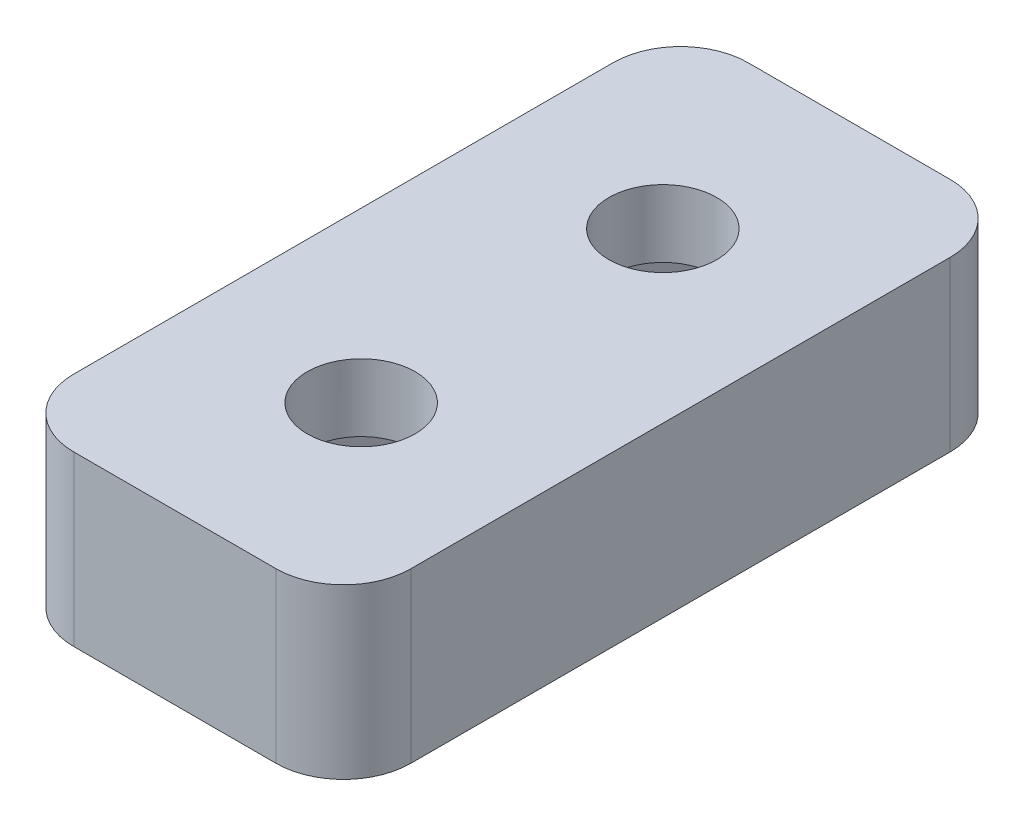
SolidWorks part; units mm, degrees
ref_plane "Alzado" through (0, 0, 0) normal (0, 0, 1) x (1, 0, 0)
ref_plane "Planta" through (0, 0, 0) normal (0, 1, 0) x (1, 0, 0)
ref_plane "Vista lateral" through (0, 0, 0) normal (1, 0, 0) x (0, 0, -1)
sketch "Croquis1" plane through (0, 0, 0) normal (0, 1, 0) x (1, 0, 0)
  line L0 (-5, 0) -> (5, 0) construction
  line L1 (-5, -10) -> (5, -10)
  line L2 (-5, -10) -> (-5, 10)
  line L3 (-5, 10) -> (5, 10)
  line L4 (5, -10) -> (5, 10)
  line L5 (-5, -10) -> (5, 10) construction
  line L6 (-5, 10) -> (5, -10) construction
  line L7 (0, 10) -> (0, -10) construction
  circle A0 centre (0, 4.4745) radius 1.6
  circle A1 centre (0, -4.4745) radius 1.6
  point P0 (0, 0)
  dimension "D3" = 3.2
  dimension "D1" = 10
  dimension "D2" = 20
extrude "Saliente-Extruir1" add sketch "Croquis1" along normal blind 5
sketch "Croquis2" plane through (0, 0, 0) normal (0, -1, 0) x (1, 0, 0)
  line L0 (-5, 0) -> (5, 0) construction
  line L1 (3.2332, 4.4745) -> (1.6166, 7.2745)
  line L2 (1.6166, 7.2745) -> (-1.6166, 7.2745)
  line L3 (-1.6166, 7.2745) -> (-3.2332, 4.4745)
  line L4 (-3.2332, 4.4745) -> (-1.6166, 1.6745)
  line L5 (-1.6166, 1.6745) -> (1.6166, 1.6745)
  line L6 (1.6166, 1.6745) -> (3.2332, 4.4745)
  line L7 (-5, -10) -> (-5, 10) construction
  line L8 (5, 10) -> (5, -10) construction
  line L9 (1.6166, -1.6745) -> (3.2332, -4.4745)
  line L10 (-1.6166, -1.6745) -> (1.6166, -1.6745)
  line L11 (-3.2332, -4.4745) -> (-1.6166, -1.6745)
  line L12 (-1.6166, -7.2745) -> (-3.2332, -4.4745)
  line L13 (1.6166, -7.2745) -> (-1.6166, -7.2745)
  line L14 (3.2332, -4.4745) -> (1.6166, -7.2745)
  circle A0 centre (0, 4.4745) radius 2.8 construction
  circle A1 centre (0, -4.4745) radius 2.8 construction
  dimension "D1" = 5.6
extrude "Cortar-Extruir1" cut sketch "Croquis2" against normal blind 3
fillet "Redondeo1" radius 2 4 edges at (-5, 2.5, 10) (5, 2.5, 10) (5, 2.5, -10) (-5, 2.5, -10)
